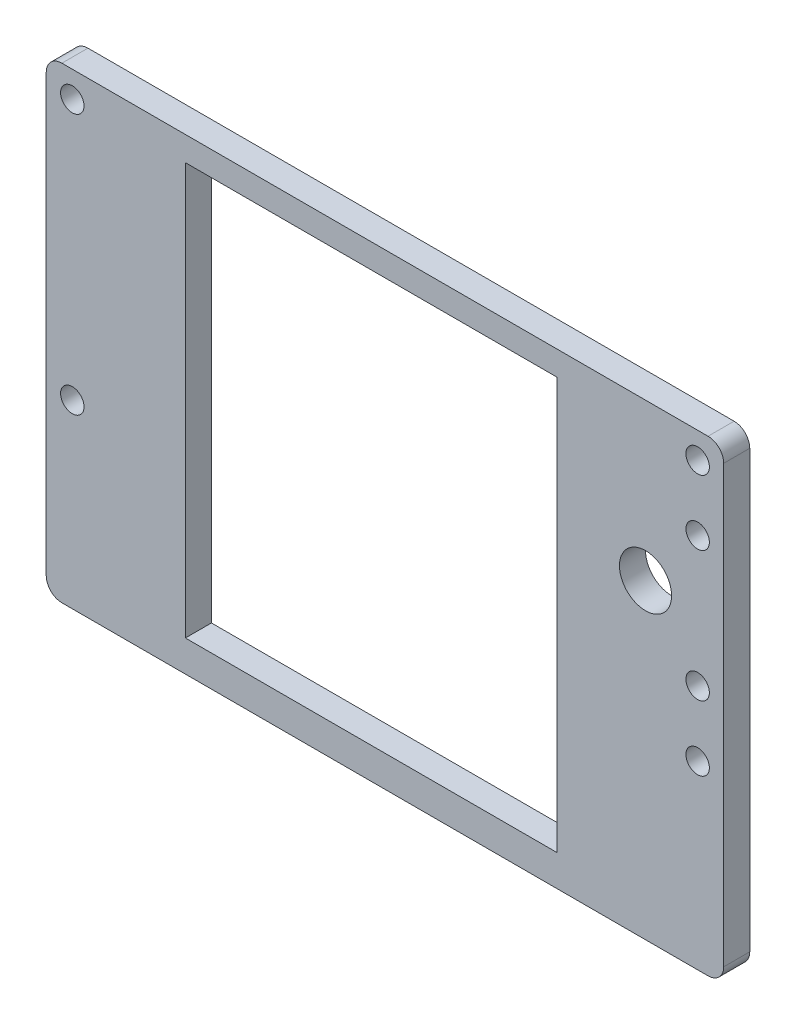
SolidWorks part; units mm, degrees
ref_plane "Front Plane" through (0, 0, 0) normal (0, 0, 1) x (1, 0, 0)
ref_plane "Top Plane" through (0, 0, 0) normal (0, 1, 0) x (1, 0, 0)
ref_plane "Right Plane" through (0, 0, 0) normal (1, 0, 0) x (0, 0, -1)
sketch "Sketch1" plane through (0, 0, 0) normal (0, 0, 1) x (1, 0, 0)
  line L1 (0, 0) -> (130, 0)
  line L2 (0, 0) -> (0, -89.6794)
  line L3 (0, -89.6794) -> (130, -89.6794)
  line L4 (130, 0) -> (130, -89.6794)
  line L6 (27.7, -82.6794) -> (27.7, -5.6794) construction
  line L8 (97, -82.6794) -> (97, -5.6794) construction
  line L9 (27.7, -5.6794) -> (97, -5.6794) construction
  line L10 (97, -82.6794) -> (27.7, -82.6794) construction
  line L11 (26.7, -4.6794) -> (98, -4.6794)
  line L12 (98, -83.6794) -> (98, -4.6794)
  line L13 (98, -83.6794) -> (26.7, -83.6794)
  line L14 (26.7, -83.6794) -> (26.7, -4.6794)
  circle A4 centre (125, -5) radius 2.25
  circle A5 centre (125, -55) radius 2.25
  circle A6 centre (5, -55) radius 2.25
  circle A7 centre (5, -5) radius 2.25
  dimension "D2" = 5
  dimension "D1" = 4.5
  dimension "D3" = 26.7
  dimension "D4" = 27.7
  dimension "D5" = 97
  dimension "D6" = 98
  dimension "D7" = 125
  dimension "D8" = 130
  dimension "D9" = 4.6794
  dimension "D10" = 5
  dimension "D11" = 5.6794
  dimension "D12" = 55
  dimension "D13" = 82.6794
  dimension "D14" = 83.6794
  dimension "D15" = 89.6794
extrude "Boss-Extrude1" add sketch "Sketch1" along normal blind 5
fillet "Fillet1" radius 3 4 edges at (130, 0, 2.5) (130, -89.6794, 2.5) (0, -89.6794, 2.5) (0, 0, 2.5)
sketch "Sketch2" plane through (0, 0, 0) normal (0, 0, -1) x (-1, 0, 0)
  line L0 (-127, 0) -> (-3, 0) construction
  line L1 (-130, -86.6794) -> (-130, -3) construction
  circle A0 centre (-115, -30) radius 5
  dimension "D1" = 10
  dimension "D2" = 30
  dimension "D3" = 15
extrude "Cut-Extrude1" cut sketch "Sketch2" against normal blind 5
sketch "Sketch3" plane through (0, 0, 5) normal (0, 0, 1) x (1, 0, 0)
  line L0 (125, -5) -> (125, -55) construction
  circle A0 centre (125, -42.5) radius 2.25
  circle A1 centre (125, -17.5) radius 2.25
  circle A2 centre (115, -30) radius 5 construction
  dimension "D1" = 4.5
  dimension "D2" = 4.5
  dimension "D3" = 25
  dimension "D4" = 12.5
extrude "Cut-Extrude2" cut sketch "Sketch3" against normal blind 5
